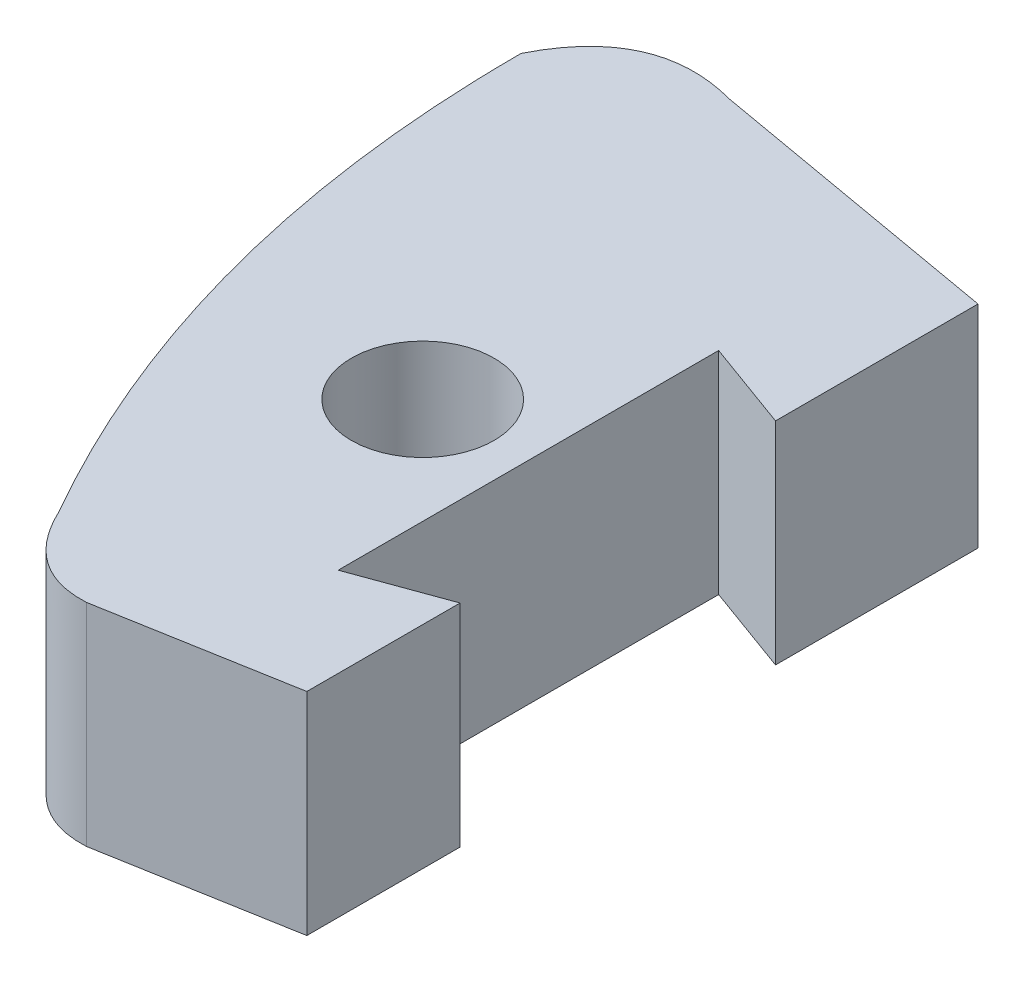
SolidWorks part; units mm, degrees
ref_plane "Front Plane" through (0, 0, 0) normal (0, 0, 1) x (1, 0, 0)
ref_plane "Top Plane" through (0, 0, 0) normal (0, 1, 0) x (1, 0, 0)
ref_plane "Right Plane" through (0, 0, 0) normal (1, 0, 0) x (0, 0, -1)
sketch "Sketch1" plane through (0, 0, 0) normal (0, 1, 0) x (1, 0, 0)
  line L0 (0, 0) -> (0, 6.35)
  line L1 (-1.7727, -0.3126) -> (0, 0)
  line L2 (0, 6.35) -> (-2.8559, 6.8536)
  line L3 (0, 1.45) -> (-0.8457, 1.1422)
  line L4 (-0.8457, 1.1422) -> (-0.8457, 4.7422)
  line L5 (-0.8457, 4.7422) -> (0, 4.4344)
  line L6 (-0.8457, 2.9422) -> (-2.3248, 2.9422) construction
  circle A1 centre (-1.8457, 2.9422) radius 0.675
  spline S0 degree 2 poles (-1.7727, -0.3126) (-2.3429, -0.3423) (-2.6469, 0.3029) knots 0 0 0 1 1 1
  spline S1 degree 2 poles (-2.6469, 0.3029) (-4.217, 3.0426) (-4.2144, 6.2424) knots 0 0 0 1 1 1
  spline S2 degree 2 poles (-4.2144, 6.2424) (-3.7829, 7.1046) (-2.8559, 6.8536) knots 0 0 0 1 1 1
  dimension "D11" = 1.35
  dimension "D1" = 6.35
  dimension "D2" = 1.8
  dimension "D3" = 100
  dimension "D4" = 2.9
  dimension "D5" = 100
  dimension "D6" = 3.6
  dimension "D7" = 0.9
  dimension "D8" = 0.9
  dimension "D9" = 110
  dimension "D10" = 1.45
  dimension "D12" = 1
extrude "Boss-Extrude1" add sketch "Sketch1" along normal blind 2
